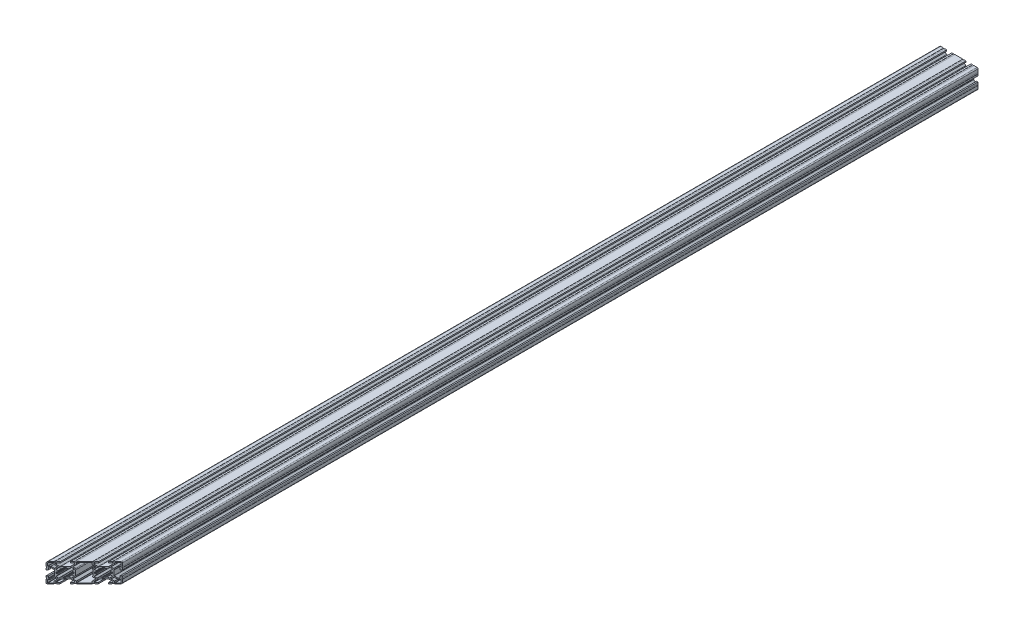
SolidWorks part; units mm, degrees
material "6063-T6, Barra (SS)"
ref_plane "Plano frontal" through (0, 0, 0) normal (0, 0, 1) x (1, 0, 0)
ref_plane "Plano superior" through (0, 0, 0) normal (0, 1, 0) x (1, 0, 0)
ref_plane "Plano direito" through (0, 0, 0) normal (1, 0, 0) x (0, 0, -1)
sketch "Esboço1" plane through (0, 0, 0) normal (1, 0, 0) x (0, 0, -1)
  line L0 (-700, 0) -> (700, 0)
  point P4 (0, 0)
  dimension "D1" = 1400
other "Retangular PF30-02 - PERFIL 3060 BÁSICO(1)"
ref_plane "Plano1" through (0, 0, 700) normal (0, 0, -1) x (0, -1, 0)
sketch "Sketch1" plane through (0, 0, 700) normal (0, 0, -1) x (0, -1, 0)
  line L0 (-4.05, 30) -> (-4.05, 28)
  line L1 (-6.0258, -23.5007) -> (-8.7121, -26.187)
  line L2 (-8.8, -26.3991) -> (-8.8, -28.4)
  line L3 (-9.1, -28.7) -> (-13.4, -28.7)
  line L4 (-13.7, -28.4) -> (-13.7, -24.1)
  line L5 (-13.4, -23.8) -> (-11.3991, -23.8)
  line L6 (-11.187, -23.7121) -> (-8.5007, -21.0258)
  line L7 (-8.0765, -21.0258) -> (-6.0258, -23.0765)
  line L8 (13.7, 5.9) -> (13.7, -5.9)
  line L9 (13.4, -6.2) -> (11.3991, -6.2)
  line L10 (11.187, -6.2879) -> (8.5007, -8.9742)
  line L11 (8.0765, -8.9742) -> (6.0258, -6.9235)
  line L12 (4.0435, -6.7) -> (-4.0435, -6.7)
  line L13 (-6.0258, -6.9235) -> (-8.0765, -8.9742)
  line L14 (-8.5007, -8.9742) -> (-11.187, -6.2879)
  line L15 (-11.3991, -6.2) -> (-13.4, -6.2)
  line L16 (-13.7, -5.9) -> (-13.7, 5.9)
  line L17 (-13.4, 6.2) -> (-11.3991, 6.2)
  line L18 (-11.187, 6.2879) -> (-8.5007, 8.9742)
  line L19 (-8.0765, 8.9742) -> (-6.0258, 6.9235)
  line L20 (-4.0435, 6.7) -> (4.0435, 6.7)
  line L21 (6.0258, 6.9235) -> (8.0765, 8.9742)
  line L22 (8.5007, 8.9742) -> (11.187, 6.2879)
  line L23 (11.3991, 6.2) -> (13.4, 6.2)
  line L24 (8.0765, 21.0258) -> (6.0258, 23.0765)
  line L25 (6.0258, 23.5007) -> (8.7121, 26.187)
  line L26 (8.8, 26.3991) -> (8.8, 28.4)
  line L27 (9.1, 28.7) -> (13.4, 28.7)
  line L28 (13.7, 28.4) -> (13.7, 24.1)
  line L29 (13.4, 23.8) -> (11.3991, 23.8)
  line L30 (11.187, 23.7121) -> (8.5007, 21.0258)
  line L31 (-8.7121, 26.187) -> (-6.0258, 23.5007)
  line L32 (-6.0258, 23.0765) -> (-8.0765, 21.0258)
  line L33 (-8.5007, 21.0258) -> (-11.187, 23.7121)
  line L34 (-11.3991, 23.8) -> (-13.4, 23.8)
  line L35 (-13.7, 24.1) -> (-13.7, 28.4)
  line L36 (-13.4, 28.7) -> (-9.1, 28.7)
  line L37 (-8.8, 28.4) -> (-8.8, 26.3991)
  line L38 (-3.0123, 9.5129) -> (-4.6823, 7.8428)
  line L39 (-5.1066, 7.8428) -> (-7.1572, 9.8934)
  line L40 (-7.1572, 10.3177) -> (-5.4871, 11.9877)
  line L41 (-6.1579, 13.75) -> (-6.7, 13.75)
  line L42 (-7, 14.05) -> (-7, 15.95)
  line L43 (-6.7, 16.25) -> (-6.1579, 16.25)
  line L44 (-5.4871, 18.0123) -> (-7.1572, 19.6823)
  line L45 (-7.1572, 20.1066) -> (-5.1066, 22.1572)
  line L46 (-4.6823, 22.1572) -> (-3.0123, 20.4871)
  line L47 (-1.25, 21.1579) -> (-1.25, 21.7)
  line L48 (-0.95, 22) -> (0.95, 22)
  line L49 (1.25, 21.7) -> (1.25, 21.1579)
  line L50 (3.0123, 20.4871) -> (4.6823, 22.1572)
  line L51 (5.1066, 22.1572) -> (7.1572, 20.1066)
  line L52 (7.1572, 19.6823) -> (5.4871, 18.0123)
  line L53 (6.1579, 16.25) -> (6.7, 16.25)
  line L54 (7, 15.95) -> (7, 14.05)
  line L55 (6.7, 13.75) -> (6.1579, 13.75)
  line L56 (5.4871, 11.9877) -> (7.1572, 10.3177)
  line L57 (7.1572, 9.8934) -> (5.1066, 7.8428)
  line L58 (4.6823, 7.8428) -> (3.0123, 9.5129)
  line L59 (1.25, 8.8421) -> (1.25, 8.3)
  line L60 (0.95, 8) -> (-0.95, 8)
  line L61 (-1.25, 8.3) -> (-1.25, 8.8421)
  line L62 (-1.25, -8.8421) -> (-1.25, -8.3)
  line L63 (-0.95, -8) -> (0.95, -8)
  line L64 (1.25, -8.3) -> (1.25, -8.8421)
  line L65 (3.0123, -9.5129) -> (4.6823, -7.8428)
  line L66 (5.1066, -7.8428) -> (7.1572, -9.8934)
  line L67 (7.1572, -10.3177) -> (5.4871, -11.9877)
  line L68 (6.1579, -13.75) -> (6.7, -13.75)
  line L69 (7, -14.05) -> (7, -15.95)
  line L70 (6.7, -16.25) -> (6.1579, -16.25)
  line L71 (5.4871, -18.0123) -> (7.1572, -19.6823)
  line L72 (7.1572, -20.1066) -> (5.1066, -22.1572)
  line L73 (4.6823, -22.1572) -> (3.0123, -20.4871)
  line L74 (1.25, -21.1579) -> (1.25, -21.7)
  line L75 (0.95, -22) -> (-0.95, -22)
  line L76 (-1.25, -21.7) -> (-1.25, -21.1579)
  line L77 (-3.0123, -20.4871) -> (-4.6823, -22.1572)
  line L78 (-5.1066, -22.1572) -> (-7.1572, -20.1066)
  line L79 (-7.1572, -19.6823) -> (-5.4871, -18.0123)
  line L80 (-6.1579, -16.25) -> (-6.7, -16.25)
  line L81 (-7, -15.95) -> (-7, -14.05)
  line L82 (-6.7, -13.75) -> (-6.1579, -13.75)
  line L83 (-5.4871, -11.9877) -> (-7.1572, -10.3177)
  line L84 (-7.1572, -9.8934) -> (-5.1066, -7.8428)
  line L85 (-4.6823, -7.8428) -> (-3.0123, -9.5129)
  line L86 (6.0258, -23.0765) -> (8.0765, -21.0258)
  line L87 (8.5007, -21.0258) -> (11.187, -23.7121)
  line L88 (11.3991, -23.8) -> (13.4, -23.8)
  line L89 (13.7, -24.1) -> (13.7, -28.4)
  line L90 (13.4, -28.7) -> (9.1, -28.7)
  line L91 (8.8, -28.4) -> (8.8, -26.3991)
  line L92 (8.7121, -26.187) -> (6.0258, -23.5007)
  line L93 (15, -6.2) -> (15, 6.2)
  line L94 (15, 6.2) -> (14.7, 6.2)
  line L95 (14.7, 6.2) -> (14.7, 8.4)
  line L96 (14.7, 8.4) -> (15, 8.4)
  line L97 (15, 8.4) -> (15, 10.95)
  line L98 (15, 10.95) -> (13, 10.95)
  line L99 (13, 10.95) -> (13, 7.8)
  line L100 (12.7, 7.5) -> (11.9376, 7.5)
  line L101 (11.7255, 7.5879) -> (8.5343, 10.779)
  line L102 (8.3, 11.3447) -> (8.3, 18.6553)
  line L103 (8.5343, 19.221) -> (11.7255, 22.4121)
  line L104 (11.9376, 22.5) -> (12.7, 22.5)
  line L105 (13, 22.2) -> (13, 19.05)
  line L106 (13, 19.05) -> (15, 19.05)
  line L107 (15, 19.05) -> (15, 21.6)
  line L108 (15, 21.6) -> (14.7, 21.6)
  line L109 (14.7, 21.6) -> (14.7, 23.8)
  line L110 (14.7, 23.8) -> (15, 23.8)
  line L111 (15, 23.8) -> (15, 28.5)
  line L112 (13.5, 30) -> (8.8, 30)
  line L113 (8.8, 30) -> (8.8, 29.7)
  line L114 (8.8, 29.7) -> (6.6, 29.7)
  line L115 (6.6, 29.7) -> (6.6, 30)
  line L116 (6.6, 30) -> (4.05, 30)
  line L117 (4.05, 30) -> (4.05, 28)
  line L118 (4.05, 28) -> (7.2, 28)
  line L119 (7.5, 27.7) -> (7.5, 26.9376)
  line L120 (7.4121, 26.7255) -> (4.221, 23.5343)
  line L121 (3.6553, 23.3) -> (-3.6553, 23.3)
  line L122 (-4.221, 23.5343) -> (-7.4121, 26.7255)
  line L123 (-7.5, 26.9376) -> (-7.5, 27.7)
  line L124 (-7.2, 28) -> (-4.05, 28)
  line L125 (-4.05, 30) -> (-6.6, 30)
  line L126 (-6.6, 30) -> (-6.6, 29.7)
  line L127 (-6.6, 29.7) -> (-8.8, 29.7)
  line L128 (-8.8, 29.7) -> (-8.8, 30)
  line L129 (-8.8, 30) -> (-13.5, 30)
  line L130 (-15, 28.5) -> (-15, 23.8)
  line L131 (-15, 23.8) -> (-14.7, 23.8)
  line L132 (-14.7, 23.8) -> (-14.7, 21.6)
  line L133 (-14.7, 21.6) -> (-15, 21.6)
  line L134 (-15, 21.6) -> (-15, 19.05)
  line L135 (-15, 19.05) -> (-13, 19.05)
  line L136 (-13, 19.05) -> (-13, 22.2)
  line L137 (-12.7, 22.5) -> (-11.9376, 22.5)
  line L138 (-11.7255, 22.4121) -> (-8.5343, 19.221)
  line L139 (-8.3, 18.6553) -> (-8.3, 11.3447)
  line L140 (-8.5343, 10.779) -> (-11.7255, 7.5879)
  line L141 (-11.9376, 7.5) -> (-12.7, 7.5)
  line L142 (-13, 7.8) -> (-13, 10.95)
  line L143 (-13, 10.95) -> (-15, 10.95)
  line L144 (-15, 10.95) -> (-15, 8.4)
  line L145 (-15, 8.4) -> (-14.7, 8.4)
  line L146 (-14.7, 8.4) -> (-14.7, 6.2)
  line L147 (-14.7, 6.2) -> (-15, 6.2)
  line L148 (-15, 6.2) -> (-15, -6.2)
  line L149 (-15, -6.2) -> (-14.7, -6.2)
  line L150 (-14.7, -6.2) -> (-14.7, -8.4)
  line L151 (-14.7, -8.4) -> (-15, -8.4)
  line L152 (-15, -8.4) -> (-15, -10.95)
  line L153 (-15, -10.95) -> (-13, -10.95)
  line L154 (-13, -10.95) -> (-13, -7.8)
  line L155 (-12.7, -7.5) -> (-11.9376, -7.5)
  line L156 (-11.7255, -7.5879) -> (-8.5343, -10.779)
  line L157 (-8.3, -11.3447) -> (-8.3, -18.6553)
  line L158 (-8.5343, -19.221) -> (-11.7255, -22.4121)
  line L159 (-11.9376, -22.5) -> (-12.7, -22.5)
  line L160 (-13, -22.2) -> (-13, -19.05)
  line L161 (-13, -19.05) -> (-15, -19.05)
  line L162 (-15, -19.05) -> (-15, -21.6)
  line L163 (-15, -21.6) -> (-14.7, -21.6)
  line L164 (-14.7, -21.6) -> (-14.7, -23.8)
  line L165 (-14.7, -23.8) -> (-15, -23.8)
  line L166 (-15, -23.8) -> (-15, -28.5)
  line L167 (-13.5, -30) -> (-8.8, -30)
  line L168 (-8.8, -30) -> (-8.8, -29.7)
  line L169 (-8.8, -29.7) -> (-6.6, -29.7)
  line L170 (-6.6, -29.7) -> (-6.6, -30)
  line L171 (-6.6, -30) -> (-4.05, -30)
  line L172 (-4.05, -30) -> (-4.05, -28)
  line L173 (-4.05, -28) -> (-7.2, -28)
  line L174 (-7.5, -27.7) -> (-7.5, -26.9376)
  line L175 (-7.4121, -26.7255) -> (-4.221, -23.5343)
  line L176 (-3.6553, -23.3) -> (3.6553, -23.3)
  line L177 (4.221, -23.5343) -> (7.4121, -26.7255)
  line L178 (7.5, -26.9376) -> (7.5, -27.7)
  line L179 (7.2, -28) -> (4.05, -28)
  line L180 (4.05, -28) -> (4.05, -30)
  line L181 (4.05, -30) -> (6.6, -30)
  line L182 (6.6, -30) -> (6.6, -29.7)
  line L183 (6.6, -29.7) -> (8.8, -29.7)
  line L184 (8.8, -29.7) -> (8.8, -30)
  line L185 (8.8, -30) -> (13.5, -30)
  line L186 (15, -28.5) -> (15, -23.8)
  line L187 (15, -23.8) -> (14.7, -23.8)
  line L188 (14.7, -23.8) -> (14.7, -21.6)
  line L189 (14.7, -21.6) -> (15, -21.6)
  line L190 (15, -21.6) -> (15, -19.05)
  line L191 (15, -19.05) -> (13, -19.05)
  line L192 (13, -19.05) -> (13, -22.2)
  line L193 (12.7, -22.5) -> (11.9376, -22.5)
  line L194 (11.7255, -22.4121) -> (8.5343, -19.221)
  line L195 (8.3, -18.6553) -> (8.3, -11.3447)
  line L196 (8.5343, -10.779) -> (11.7255, -7.5879)
  line L197 (11.9376, -7.5) -> (12.7, -7.5)
  line L198 (13, -7.8) -> (13, -10.95)
  line L199 (13, -10.95) -> (15, -10.95)
  line L200 (15, -10.95) -> (15, -8.4)
  line L201 (15, -8.4) -> (14.7, -8.4)
  line L202 (14.7, -8.4) -> (14.7, -6.2)
  line L203 (14.7, -6.2) -> (15, -6.2)
  arc A0 (-8.7121, -26.187) -> (-8.8, -26.3991) centre (-8.5, -26.3991) ccw
  arc A1 (-9.1, -28.7) -> (-8.8, -28.4) centre (-9.1, -28.4) ccw
  arc A2 (-13.7, -28.4) -> (-13.4, -28.7) centre (-13.4, -28.4) ccw
  arc A3 (-13.4, -23.8) -> (-13.7, -24.1) centre (-13.4, -24.1) ccw
  arc A4 (-11.3991, -23.8) -> (-11.187, -23.7121) centre (-11.3991, -23.5) ccw
  arc A5 (-8.0765, -21.0258) -> (-8.5007, -21.0258) centre (-8.2886, -21.238) ccw
  arc A6 (-6.0258, -23.5007) -> (-6.0258, -23.0765) centre (-6.238, -23.2886) ccw
  arc A7 (13.4, -6.2) -> (13.7, -5.9) centre (13.4, -5.9) ccw
  arc A8 (11.3991, -6.2) -> (11.187, -6.2879) centre (11.3991, -6.5) ccw
  arc A9 (8.0765, -8.9742) -> (8.5007, -8.9742) centre (8.2886, -8.762) ccw
  arc A10 (6.0258, -6.9235) -> (4.0435, -6.7) centre (4.8945, -8.0549) ccw
  arc A11 (-4.0435, -6.7) -> (-6.0258, -6.9235) centre (-4.8945, -8.0549) ccw
  arc A12 (-8.5007, -8.9742) -> (-8.0765, -8.9742) centre (-8.2886, -8.762) ccw
  arc A13 (-11.187, -6.2879) -> (-11.3991, -6.2) centre (-11.3991, -6.5) ccw
  arc A14 (-13.7, -5.9) -> (-13.4, -6.2) centre (-13.4, -5.9) ccw
  arc A15 (-13.4, 6.2) -> (-13.7, 5.9) centre (-13.4, 5.9) ccw
  arc A16 (-11.3991, 6.2) -> (-11.187, 6.2879) centre (-11.3991, 6.5) ccw
  arc A17 (-8.0765, 8.9742) -> (-8.5007, 8.9742) centre (-8.2886, 8.762) ccw
  arc A18 (-6.0258, 6.9235) -> (-4.0435, 6.7) centre (-4.8945, 8.0549) ccw
  arc A19 (4.0435, 6.7) -> (6.0258, 6.9235) centre (4.8945, 8.0549) ccw
  arc A20 (8.5007, 8.9742) -> (8.0765, 8.9742) centre (8.2886, 8.762) ccw
  arc A21 (11.187, 6.2879) -> (11.3991, 6.2) centre (11.3991, 6.5) ccw
  arc A22 (13.7, 5.9) -> (13.4, 6.2) centre (13.4, 5.9) ccw
  arc A23 (6.0258, 23.5007) -> (6.0258, 23.0765) centre (6.238, 23.2886) ccw
  arc A24 (8.7121, 26.187) -> (8.8, 26.3991) centre (8.5, 26.3991) ccw
  arc A25 (9.1, 28.7) -> (8.8, 28.4) centre (9.1, 28.4) ccw
  arc A26 (13.7, 28.4) -> (13.4, 28.7) centre (13.4, 28.4) ccw
  arc A27 (13.4, 23.8) -> (13.7, 24.1) centre (13.4, 24.1) ccw
  arc A28 (11.3991, 23.8) -> (11.187, 23.7121) centre (11.3991, 23.5) ccw
  arc A29 (8.0765, 21.0258) -> (8.5007, 21.0258) centre (8.2886, 21.238) ccw
  arc A30 (-6.0258, 23.0765) -> (-6.0258, 23.5007) centre (-6.238, 23.2886) ccw
  arc A31 (-8.5007, 21.0258) -> (-8.0765, 21.0258) centre (-8.2886, 21.238) ccw
  arc A32 (-11.187, 23.7121) -> (-11.3991, 23.8) centre (-11.3991, 23.5) ccw
  arc A33 (-13.7, 24.1) -> (-13.4, 23.8) centre (-13.4, 24.1) ccw
  arc A34 (-13.4, 28.7) -> (-13.7, 28.4) centre (-13.4, 28.4) ccw
  arc A35 (-8.8, 28.4) -> (-9.1, 28.7) centre (-9.1, 28.4) ccw
  arc A36 (-8.8, 26.3991) -> (-8.7121, 26.187) centre (-8.5, 26.3991) ccw
  arc A37 (-2.6678, 9.57) -> (-3.0123, 9.5129) centre (-2.8001, 9.3007) ccw
  arc A38 (-5.1066, 7.8428) -> (-4.6823, 7.8428) centre (-4.8945, 8.0549) ccw
  arc A39 (-7.1572, 10.3177) -> (-7.1572, 9.8934) centre (-6.9451, 10.1055) ccw
  arc A40 (-5.4871, 11.9877) -> (-5.43, 12.3322) centre (-5.6993, 12.1999) ccw
  arc A41 (-5.867, 13.5232) -> (-5.43, 12.3322) centre (0, 15) ccw
  arc A42 (-5.867, 13.5232) -> (-6.1579, 13.75) centre (-6.1579, 13.45) ccw
  arc A43 (-7, 14.05) -> (-6.7, 13.75) centre (-6.7, 14.05) ccw
  arc A44 (-6.7, 16.25) -> (-7, 15.95) centre (-6.7, 15.95) ccw
  arc A45 (-6.1579, 16.25) -> (-5.867, 16.4768) centre (-6.1579, 16.55) ccw
  arc A46 (-5.43, 17.6678) -> (-5.867, 16.4768) centre (0, 15) ccw
  arc A47 (-5.43, 17.6678) -> (-5.4871, 18.0123) centre (-5.6993, 17.8001) ccw
  arc A48 (-7.1572, 20.1066) -> (-7.1572, 19.6823) centre (-6.9451, 19.8945) ccw
  arc A49 (-4.6823, 22.1572) -> (-5.1066, 22.1572) centre (-4.8945, 21.9451) ccw
  arc A50 (-3.0123, 20.4871) -> (-2.6678, 20.43) centre (-2.8001, 20.6993) ccw
  arc A51 (-1.4768, 20.867) -> (-2.6678, 20.43) centre (0, 15) ccw
  arc A52 (-1.4768, 20.867) -> (-1.25, 21.1579) centre (-1.55, 21.1579) ccw
  arc A53 (-0.95, 22) -> (-1.25, 21.7) centre (-0.95, 21.7) ccw
  arc A54 (1.25, 21.7) -> (0.95, 22) centre (0.95, 21.7) ccw
  arc A55 (1.25, 21.1579) -> (1.4768, 20.867) centre (1.55, 21.1579) ccw
  arc A56 (2.6678, 20.43) -> (1.4768, 20.867) centre (0, 15) ccw
  arc A57 (2.6678, 20.43) -> (3.0123, 20.4871) centre (2.8001, 20.6993) ccw
  arc A58 (5.1066, 22.1572) -> (4.6823, 22.1572) centre (4.8945, 21.9451) ccw
  arc A59 (7.1572, 19.6823) -> (7.1572, 20.1066) centre (6.9451, 19.8945) ccw
  arc A60 (5.4871, 18.0123) -> (5.43, 17.6678) centre (5.6993, 17.8001) ccw
  arc A61 (5.867, 16.4768) -> (5.43, 17.6678) centre (0, 15) ccw
  arc A62 (5.867, 16.4768) -> (6.1579, 16.25) centre (6.1579, 16.55) ccw
  arc A63 (7, 15.95) -> (6.7, 16.25) centre (6.7, 15.95) ccw
  arc A64 (6.7, 13.75) -> (7, 14.05) centre (6.7, 14.05) ccw
  arc A65 (6.1579, 13.75) -> (5.867, 13.5232) centre (6.1579, 13.45) ccw
  arc A66 (5.43, 12.3322) -> (5.867, 13.5232) centre (0, 15) ccw
  arc A67 (5.43, 12.3322) -> (5.4871, 11.9877) centre (5.6993, 12.1999) ccw
  arc A68 (7.1572, 9.8934) -> (7.1572, 10.3177) centre (6.9451, 10.1055) ccw
  arc A69 (4.6823, 7.8428) -> (5.1066, 7.8428) centre (4.8945, 8.0549) ccw
  arc A70 (3.0123, 9.5129) -> (2.6678, 9.57) centre (2.8001, 9.3007) ccw
  arc A71 (1.4768, 9.133) -> (2.6678, 9.57) centre (0, 15) ccw
  arc A72 (1.4768, 9.133) -> (1.25, 8.8421) centre (1.55, 8.8421) ccw
  arc A73 (0.95, 8) -> (1.25, 8.3) centre (0.95, 8.3) ccw
  arc A74 (-1.25, 8.3) -> (-0.95, 8) centre (-0.95, 8.3) ccw
  arc A75 (-1.25, 8.8421) -> (-1.4768, 9.133) centre (-1.55, 8.8421) ccw
  arc A76 (-2.6678, 9.57) -> (-1.4768, 9.133) centre (0, 15) ccw
  arc A77 (-3.0123, -9.5129) -> (-2.6678, -9.57) centre (-2.8001, -9.3007) ccw
  arc A78 (-1.4768, -9.133) -> (-2.6678, -9.57) centre (0, -15) ccw
  arc A79 (-1.4768, -9.133) -> (-1.25, -8.8421) centre (-1.55, -8.8421) ccw
  arc A80 (-0.95, -8) -> (-1.25, -8.3) centre (-0.95, -8.3) ccw
  arc A81 (1.25, -8.3) -> (0.95, -8) centre (0.95, -8.3) ccw
  arc A82 (1.25, -8.8421) -> (1.4768, -9.133) centre (1.55, -8.8421) ccw
  arc A83 (2.6678, -9.57) -> (1.4768, -9.133) centre (0, -15) ccw
  arc A84 (2.6678, -9.57) -> (3.0123, -9.5129) centre (2.8001, -9.3007) ccw
  arc A85 (5.1066, -7.8428) -> (4.6823, -7.8428) centre (4.8945, -8.0549) ccw
  arc A86 (7.1572, -10.3177) -> (7.1572, -9.8934) centre (6.9451, -10.1055) ccw
  arc A87 (5.4871, -11.9877) -> (5.43, -12.3322) centre (5.6993, -12.1999) ccw
  arc A88 (5.867, -13.5232) -> (5.43, -12.3322) centre (0, -15) ccw
  arc A89 (5.867, -13.5232) -> (6.1579, -13.75) centre (6.1579, -13.45) ccw
  arc A90 (7, -14.05) -> (6.7, -13.75) centre (6.7, -14.05) ccw
  arc A91 (6.7, -16.25) -> (7, -15.95) centre (6.7, -15.95) ccw
  arc A92 (6.1579, -16.25) -> (5.867, -16.4768) centre (6.1579, -16.55) ccw
  arc A93 (5.43, -17.6678) -> (5.867, -16.4768) centre (0, -15) ccw
  arc A94 (5.43, -17.6678) -> (5.4871, -18.0123) centre (5.6993, -17.8001) ccw
  arc A95 (7.1572, -20.1066) -> (7.1572, -19.6823) centre (6.9451, -19.8945) ccw
  arc A96 (4.6823, -22.1572) -> (5.1066, -22.1572) centre (4.8945, -21.9451) ccw
  arc A97 (3.0123, -20.4871) -> (2.6678, -20.43) centre (2.8001, -20.6993) ccw
  arc A98 (1.4768, -20.867) -> (2.6678, -20.43) centre (0, -15) ccw
  arc A99 (1.4768, -20.867) -> (1.25, -21.1579) centre (1.55, -21.1579) ccw
  arc A100 (0.95, -22) -> (1.25, -21.7) centre (0.95, -21.7) ccw
  arc A101 (-1.25, -21.7) -> (-0.95, -22) centre (-0.95, -21.7) ccw
  arc A102 (-1.25, -21.1579) -> (-1.4768, -20.867) centre (-1.55, -21.1579) ccw
  arc A103 (-2.6678, -20.43) -> (-1.4768, -20.867) centre (0, -15) ccw
  arc A104 (-2.6678, -20.43) -> (-3.0123, -20.4871) centre (-2.8001, -20.6993) ccw
  arc A105 (-5.1066, -22.1572) -> (-4.6823, -22.1572) centre (-4.8945, -21.9451) ccw
  arc A106 (-7.1572, -19.6823) -> (-7.1572, -20.1066) centre (-6.9451, -19.8945) ccw
  arc A107 (-5.4871, -18.0123) -> (-5.43, -17.6678) centre (-5.6993, -17.8001) ccw
  arc A108 (-5.867, -16.4768) -> (-5.43, -17.6678) centre (0, -15) ccw
  arc A109 (-5.867, -16.4768) -> (-6.1579, -16.25) centre (-6.1579, -16.55) ccw
  arc A110 (-7, -15.95) -> (-6.7, -16.25) centre (-6.7, -15.95) ccw
  arc A111 (-6.7, -13.75) -> (-7, -14.05) centre (-6.7, -14.05) ccw
  arc A112 (-6.1579, -13.75) -> (-5.867, -13.5232) centre (-6.1579, -13.45) ccw
  arc A113 (-5.43, -12.3322) -> (-5.867, -13.5232) centre (0, -15) ccw
  arc A114 (-5.43, -12.3322) -> (-5.4871, -11.9877) centre (-5.6993, -12.1999) ccw
  arc A115 (-7.1572, -9.8934) -> (-7.1572, -10.3177) centre (-6.9451, -10.1055) ccw
  arc A116 (-4.6823, -7.8428) -> (-5.1066, -7.8428) centre (-4.8945, -8.0549) ccw
  arc A117 (8.5007, -21.0258) -> (8.0765, -21.0258) centre (8.2886, -21.238) ccw
  arc A118 (11.187, -23.7121) -> (11.3991, -23.8) centre (11.3991, -23.5) ccw
  arc A119 (13.7, -24.1) -> (13.4, -23.8) centre (13.4, -24.1) ccw
  arc A120 (13.4, -28.7) -> (13.7, -28.4) centre (13.4, -28.4) ccw
  arc A121 (8.8, -28.4) -> (9.1, -28.7) centre (9.1, -28.4) ccw
  arc A122 (8.8, -26.3991) -> (8.7121, -26.187) centre (8.5, -26.3991) ccw
  arc A123 (6.0258, -23.0765) -> (6.0258, -23.5007) centre (6.238, -23.2886) ccw
  arc A124 (12.7, 7.5) -> (13, 7.8) centre (12.7, 7.8) ccw
  arc A125 (11.7255, 7.5879) -> (11.9376, 7.5) centre (11.9376, 7.8) ccw
  arc A126 (8.3, 11.3447) -> (8.5343, 10.779) centre (9.1, 11.3447) ccw
  arc A127 (8.5343, 19.221) -> (8.3, 18.6553) centre (9.1, 18.6553) ccw
  arc A128 (11.9376, 22.5) -> (11.7255, 22.4121) centre (11.9376, 22.2) ccw
  arc A129 (13, 22.2) -> (12.7, 22.5) centre (12.7, 22.2) ccw
  arc A130 (15, 28.5) -> (13.5, 30) centre (13.5, 28.5) ccw
  arc A131 (7.5, 27.7) -> (7.2, 28) centre (7.2, 27.7) ccw
  arc A132 (7.4121, 26.7255) -> (7.5, 26.9376) centre (7.2, 26.9376) ccw
  arc A133 (3.6553, 23.3) -> (4.221, 23.5343) centre (3.6553, 24.1) ccw
  arc A134 (-4.221, 23.5343) -> (-3.6553, 23.3) centre (-3.6553, 24.1) ccw
  arc A135 (-7.5, 26.9376) -> (-7.4121, 26.7255) centre (-7.2, 26.9376) ccw
  arc A136 (-7.2, 28) -> (-7.5, 27.7) centre (-7.2, 27.7) ccw
  arc A137 (-13.5, 30) -> (-15, 28.5) centre (-13.5, 28.5) ccw
  arc A138 (-12.7, 22.5) -> (-13, 22.2) centre (-12.7, 22.2) ccw
  arc A139 (-11.7255, 22.4121) -> (-11.9376, 22.5) centre (-11.9376, 22.2) ccw
  arc A140 (-8.3, 18.6553) -> (-8.5343, 19.221) centre (-9.1, 18.6553) ccw
  arc A141 (-8.5343, 10.779) -> (-8.3, 11.3447) centre (-9.1, 11.3447) ccw
  arc A142 (-11.9376, 7.5) -> (-11.7255, 7.5879) centre (-11.9376, 7.8) ccw
  arc A143 (-13, 7.8) -> (-12.7, 7.5) centre (-12.7, 7.8) ccw
  arc A144 (-12.7, -7.5) -> (-13, -7.8) centre (-12.7, -7.8) ccw
  arc A145 (-11.7255, -7.5879) -> (-11.9376, -7.5) centre (-11.9376, -7.8) ccw
  arc A146 (-8.3, -11.3447) -> (-8.5343, -10.779) centre (-9.1, -11.3447) ccw
  arc A147 (-8.5343, -19.221) -> (-8.3, -18.6553) centre (-9.1, -18.6553) ccw
  arc A148 (-11.9376, -22.5) -> (-11.7255, -22.4121) centre (-11.9376, -22.2) ccw
  arc A149 (-13, -22.2) -> (-12.7, -22.5) centre (-12.7, -22.2) ccw
  arc A150 (-15, -28.5) -> (-13.5, -30) centre (-13.5, -28.5) ccw
  arc A151 (-7.5, -27.7) -> (-7.2, -28) centre (-7.2, -27.7) ccw
  arc A152 (-7.4121, -26.7255) -> (-7.5, -26.9376) centre (-7.2, -26.9376) ccw
  arc A153 (-3.6553, -23.3) -> (-4.221, -23.5343) centre (-3.6553, -24.1) ccw
  arc A154 (4.221, -23.5343) -> (3.6553, -23.3) centre (3.6553, -24.1) ccw
  arc A155 (7.5, -26.9376) -> (7.4121, -26.7255) centre (7.2, -26.9376) ccw
  arc A156 (7.2, -28) -> (7.5, -27.7) centre (7.2, -27.7) ccw
  arc A157 (13.5, -30) -> (15, -28.5) centre (13.5, -28.5) ccw
  arc A158 (12.7, -22.5) -> (13, -22.2) centre (12.7, -22.2) ccw
  arc A159 (11.7255, -22.4121) -> (11.9376, -22.5) centre (11.9376, -22.2) ccw
  arc A160 (8.3, -18.6553) -> (8.5343, -19.221) centre (9.1, -18.6553) ccw
  arc A161 (8.5343, -10.779) -> (8.3, -11.3447) centre (9.1, -11.3447) ccw
  arc A162 (11.9376, -7.5) -> (11.7255, -7.5879) centre (11.9376, -7.8) ccw
  arc A163 (13, -7.8) -> (12.7, -7.5) centre (12.7, -7.8) ccw
  point P0 (-15, 30)
  point P1 (0, 30)
  point P2 (15, 30)
  point P3 (15, 15)
  point P4 (15, 0)
  point P5 (15, -15)
  point P6 (15, -30)
  point P7 (0, -30)
  point P8 (-15, -30)
  point P9 (-15, -15)
  point P10 (-15, 0)
  point P11 (-15, 15)
  point P12 (0, 0)
  point P13 (0, 15)
  point P14 (0, -15)
  point P529 (0, 0)
sketch "Croquis1" plane through (0, 0, 0) normal (0, 1, 0) x (1, 0, 0)
  line L0 (-30, -700) -> (30, -640)
  line L1 (30, 700) -> (30, -700) construction
  line L2 (30, -640) -> (30, -700)
  line L3 (30, -700) -> (-30, -700)
  dimension "D1" = 45
extrude "Cortar-Extruir1" cut sketch "Croquis1" against normal through all both and the other way through all
